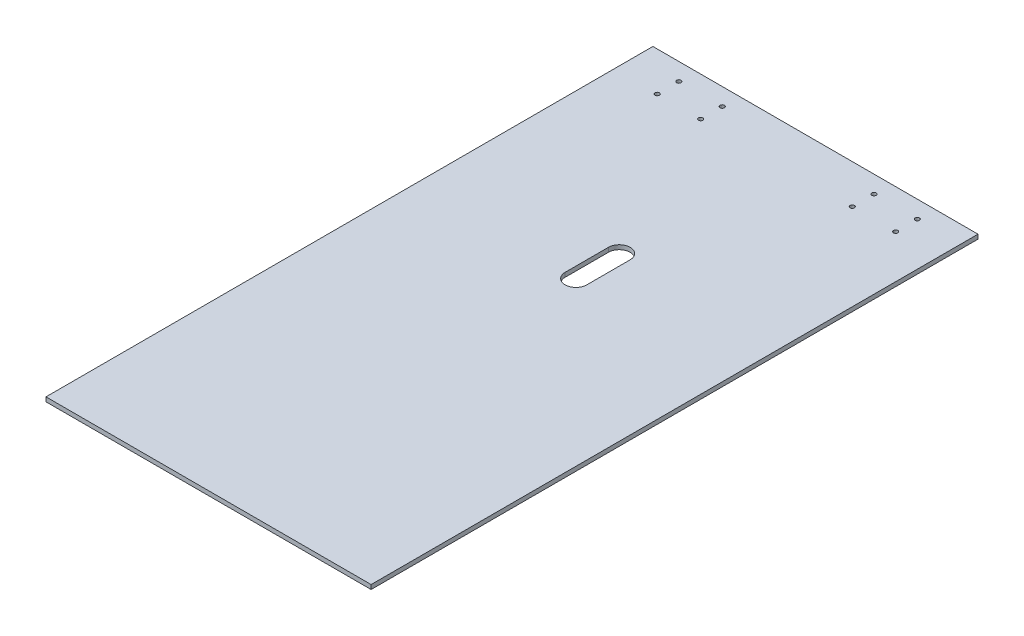
SolidWorks part; units mm, degrees
ref_plane "前视基准面" through (0, 0, 0) normal (0, 0, 1) x (1, 0, 0)
ref_plane "上视基准面" through (0, 0, 0) normal (0, 1, 0) x (1, 0, 0)
ref_plane "右视基准面" through (0, 0, 0) normal (1, 0, 0) x (0, 0, -1)
sketch "草图1" plane through (0, 0, 0) normal (0, 1, 0) x (1, 0, 0)
  line L1 (-75, 140) -> (75, 140)
  line L2 (-75, 140) -> (-75, -140)
  line L3 (-75, -140) -> (75, -140)
  line L4 (75, 140) -> (75, -140)
  line L5 (-75, 140) -> (75, -140) construction
  line L6 (-75, -140) -> (75, 140) construction
  point P0 (0, 0)
  dimension "D1" = 150
  dimension "D2" = 280
extrude "凸台-拉伸1" add sketch "草图1" along normal blind 2
ref_plane "基准面1" through (0, 0, 0) normal (-1, 0, 0) x (0, 0, 1)
sketch "草图4" plane through (0, 2, 0) normal (0, 1, 0) x (1, 0, 0)
  line L0 (75, 140) -> (-75, 140) construction
  line L1 (-75, 140) -> (-75, -140) construction
  circle A0 centre (-55, 132) radius 1
  dimension "D1" = 2
  dimension "D2" = 8
  dimension "D3" = 20
extrude "切除-拉伸1" cut sketch "草图4" against normal up to next (2 mm away)
pattern_linear "阵列(线性)1" count 2 spacing 20 along (1, 0, 0) count 2 spacing 10 along (0, 0, 1) of "切除-拉伸1"
mirror "镜向2" about plane through (0, 0, 0) normal (-1, 0, 0) of "阵列(线性)1", "切除-拉伸1"
sketch "草图5" plane through (0, 2, 0) normal (0, 1, 0) x (1, 0, 0)
  line L0 (75, -140) -> (75, 140) construction
  line L2 (5, 49.5) -> (5, 29.5)
  line L4 (-5, 49.5) -> (-5, 29.5)
  line L5 (75, 140) -> (-75, 140) construction
  line L6 (5, 39.5) -> (-5, 39.5) construction
  arc A0 (5, 49.5) -> (-5, 49.5) centre (0, 49.5) ccw
  arc A1 (-5, 29.5) -> (5, 29.5) centre (0, 29.5) ccw
  point P0 (0, 39.5)
  dimension "D3" = 75
  dimension "D1" = 20
  dimension "D2" = 10
  dimension "D4" = 100.5
extrude "切除-拉伸2" cut sketch "草图5" against normal blind 10
